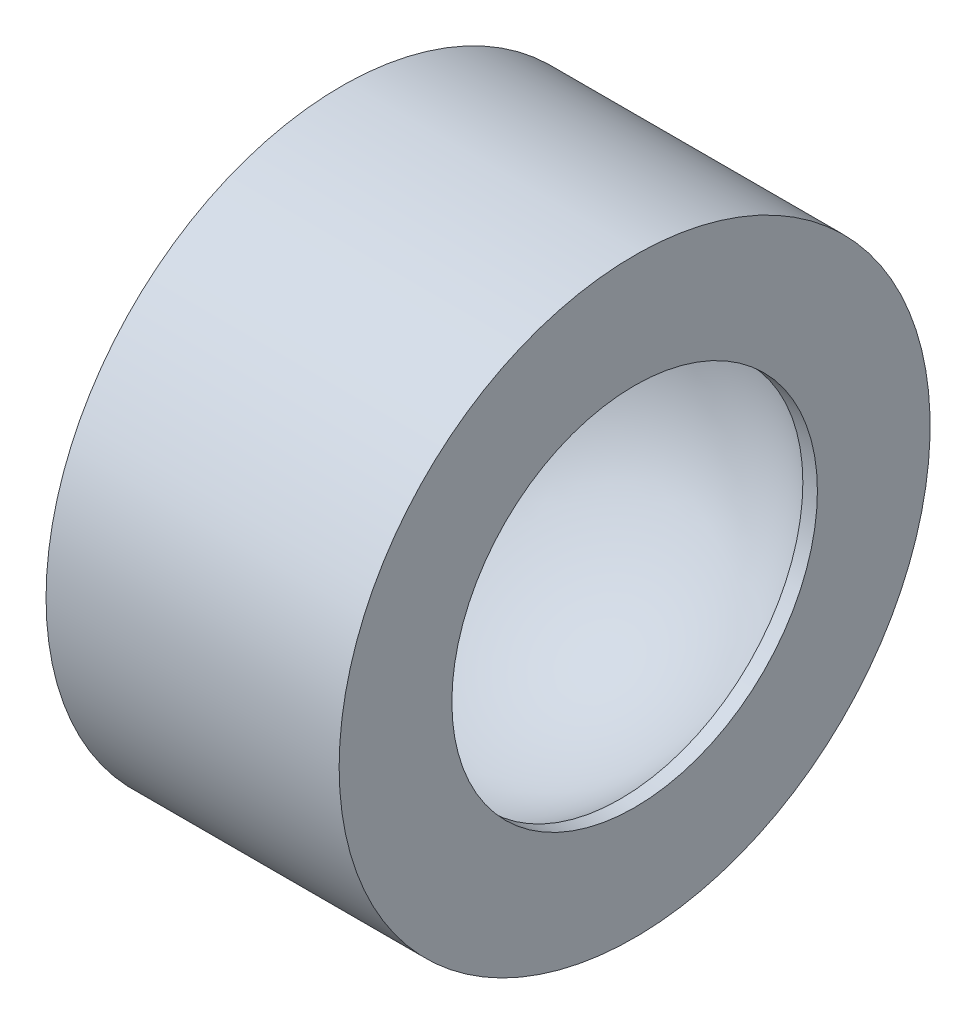
SolidWorks part; units mm, degrees
ref_plane "Front Plane" through (0, 0, 0) normal (0, 0, 1) x (1, 0, 0)
ref_plane "Top Plane" through (0, 0, 0) normal (0, 1, 0) x (1, 0, 0)
ref_plane "Right Plane" through (0, 0, 0) normal (1, 0, 0) x (0, 0, -1)
sketch "Sketch1" plane through (0, 0, 0) normal (0, 0, 1) x (1, 0, 0)
  line L0 (-12.3884, 0) -> (-5.8545, 0) construction
  line L1 (5.8545, 0) -> (15.6696, 0) construction
  line L2 (6.5, 5) -> (-6.5, 5)
  line L3 (6.5, 5) -> (6.5, 0)
  line L4 (6.5, 0) -> (5.8545, 0)
  line L5 (-6.5, 5) -> (-6.5, 0)
  line L6 (6.5, 5) -> (-6.5, 0) construction
  line L7 (6.5, 0) -> (-6.5, 5) construction
  line L8 (-5.8545, 0) -> (-6.5, 0)
  line L9 (-17.08, -8.1071) -> (20.6558, -8.1071) construction
  arc A0 (-5.8545, 0) -> (5.8545, 0) centre (0, -8.1071) cw
  point P3 (0, 2.5)
  point P13 (0, 0)
  dimension "D3" = 10
  dimension "D1" = 13
  dimension "D2" = 5
revolve "Revolve1" add sketch "Sketch1" angle 360 about L9
